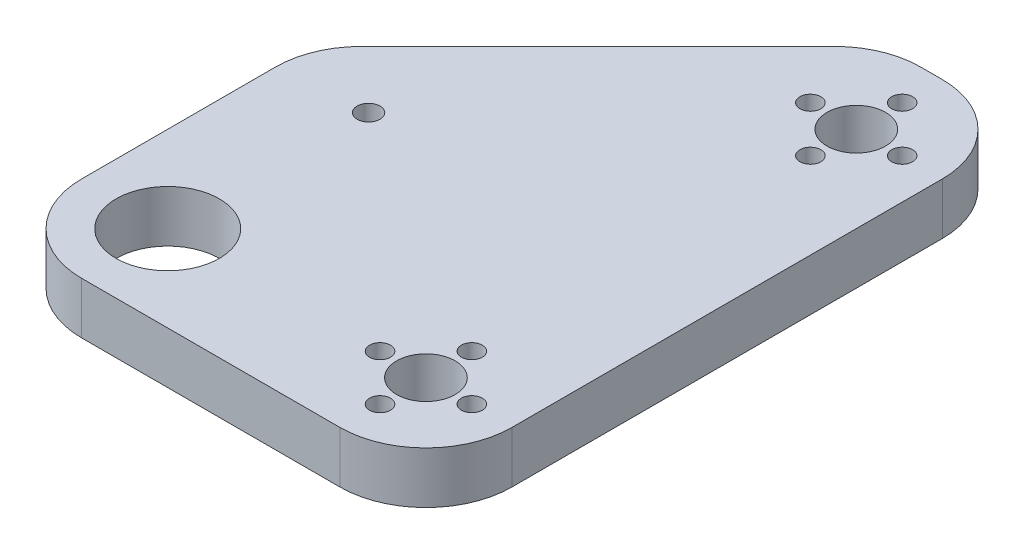
SolidWorks part; units mm, degrees
ref_plane "Front Plane" through (0, 0, 0) normal (0, 0, 1) x (1, 0, 0)
ref_plane "Top Plane" through (0, 0, 0) normal (0, 1, 0) x (1, 0, 0)
ref_plane "Right Plane" through (0, 0, 0) normal (1, 0, 0) x (0, 0, -1)
sketch "Sketch1" plane through (0, 0, 0) normal (0, 1, 0) x (1, 0, 0)
  line L1 (0, 0) -> (75, 0)
  line L2 (0, 0) -> (0, 105)
  line L3 (0, 105) -> (75, 105)
  line L4 (75, 0) -> (75, 105)
  dimension "D1" = 105
  dimension "D2" = 75
extrude "Boss-Extrude1" add sketch "Sketch1" along normal blind 9
sketch "Sketch2" plane through (0, 9, 0) normal (0, 1, 0) x (1, 0, 0)
  line L0 (0, 105) -> (0, 0) construction
  line L1 (0, 0) -> (75, 0) construction
  circle A0 centre (15, 15) radius 9
  circle A1 centre (15, 50) radius 2
  circle A2 centre (15, 50) radius 15 construction
  circle A3 centre (15, 15) radius 15 construction
  circle A4 centre (60, 15) radius 5.1
  circle A5 centre (60, 15) radius 8 construction
  circle A6 centre (60, 23) radius 1.825
  circle A7 centre (60, 7) radius 1.825
  circle A8 centre (68, 15) radius 1.825
  circle A9 centre (52, 15) radius 1.825
  circle A10 centre (60, 15) radius 11 construction
  circle A11 centre (60, 90) radius 5.1
  circle A12 centre (60, 90) radius 8 construction
  circle A13 centre (60, 98) radius 1.825
  circle A14 centre (60, 82) radius 1.825
  circle A15 centre (68, 90) radius 1.825
  circle A16 centre (52, 90) radius 1.825
  circle A17 centre (60, 90) radius 11 construction
  dimension "D1" = 18
  dimension "D2" = 4
  dimension "D3" = 30
  dimension "D4" = 30
  dimension "D6" = 10.2
  dimension "D9" = 3.65
  dimension "D10" = 3.65
  dimension "D11" = 3.65
  dimension "D12" = 22
  dimension "D7" = 16
  dimension "D8" = 10.2
  dimension "D14" = 3.65
  dimension "D15" = 3.65
  dimension "D16" = 3.65
  dimension "D17" = 16
  dimension "D18" = 22
  dimension "D19" = 3.65
  dimension "D20" = 3.65
  dimension "D5" = 35
  dimension "D13" = 45
  dimension "D21" = 75
extrude "Cut-Extrude1" cut sketch "Sketch2" against normal blind 9
chamfer "Chamfer1" distance 50 angle 45 1 edges at (0, 4.5, -105)
fillet "Fillet1" radius 15 5 edges at (75, 4.5, -105) (50, 4.5, -105) (0, 4.5, -55) (75, 4.5, 0) (0, 4.5, 0)
equation "\"D9@Sketch2\"=\"D19@Sketch2\""
equation "\"D10@Sketch2\"=\"D19@Sketch2\""
equation "\"D11@Sketch2\"=\"D19@Sketch2\""
equation "\"D16@Sketch2\"=\"D19@Sketch2\""
equation "\"D15@Sketch2\"=\"D19@Sketch2\""
equation "\"D14@Sketch2\"=\"D19@Sketch2\""
equation "\"D20@Sketch2\"=\"D19@Sketch2\""
